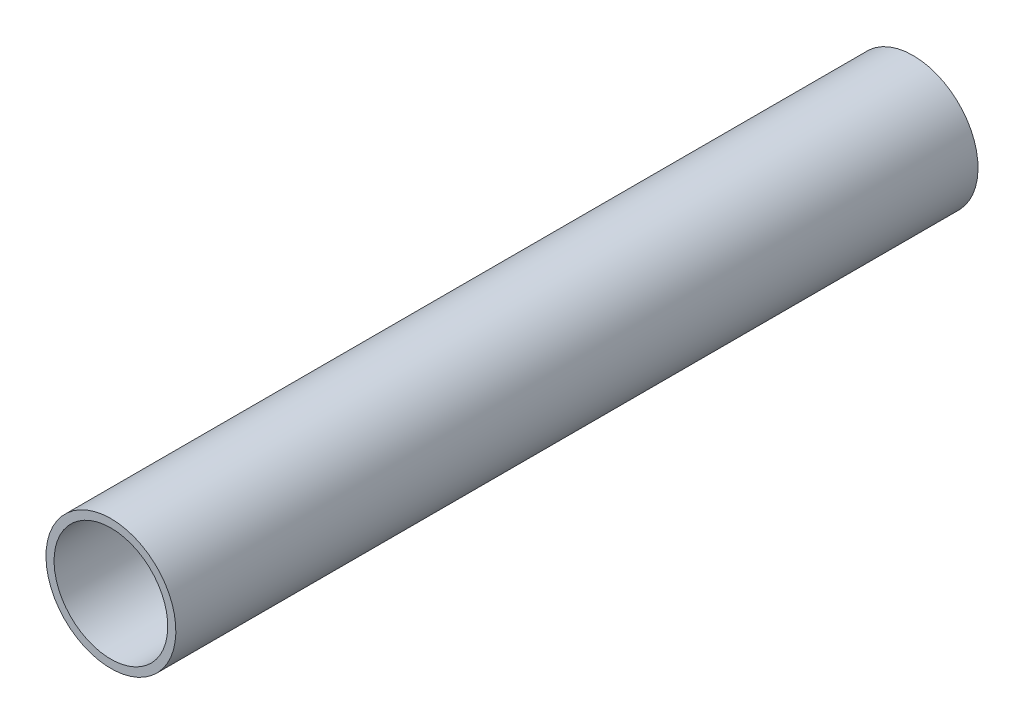
SolidWorks part; units mm, degrees
material "PE High Density"
ref_plane "Front Plane" through (0, 0, 0) normal (0, 0, 1) x (1, 0, 0)
ref_plane "Top Plane" through (0, 0, 0) normal (0, 1, 0) x (1, 0, 0)
ref_plane "Right Plane" through (0, 0, 0) normal (1, 0, 0) x (0, 0, -1)
sketch "Sketch2" plane through (0, 0, 0) normal (1, 0, 0) x (0, 0, -1)
  line L0 (17.9701, 0) -> (-700.436, 0) construction
  line L2 (-1000, 141.732) -> (1000, 141.732)
  line L3 (-1000, 141.732) -> (-1000, 161.925)
  line L4 (-1000, 161.925) -> (1000, 161.925)
  line L5 (1000, 141.732) -> (1000, 161.925)
  point P7 (0, 141.732)
  dimension "D1" = 141.732
  dimension "D3" = 2000
  dimension "D2" = 161.925
revolve "Revolve1" add sketch "Sketch2" angle 360 about L0
ref_plane "Midplane" through (0, 0, 0) normal (0, 0, 1) x (1, 0, 0)
ref_plane "Plane1" [suppressed] through (0, 0, -1000) normal (0, 0, -1) x (-1, 0, 0)
ref_plane "Plane2" [suppressed] through (0, 0, 1000) normal (0, 0, 1) x (1, 0, 0)
equation "\"ID\"= 11.160in"
equation "\"OD\"= 12.75in"
equation "\"Length\"= 2m"
equation "\"D3@Sketch2\"=\"Length\""
equation "\"D2@Sketch2\"=\"OD\"/2"
equation "\"D1@Sketch2\" = \"ID\" / 2"
